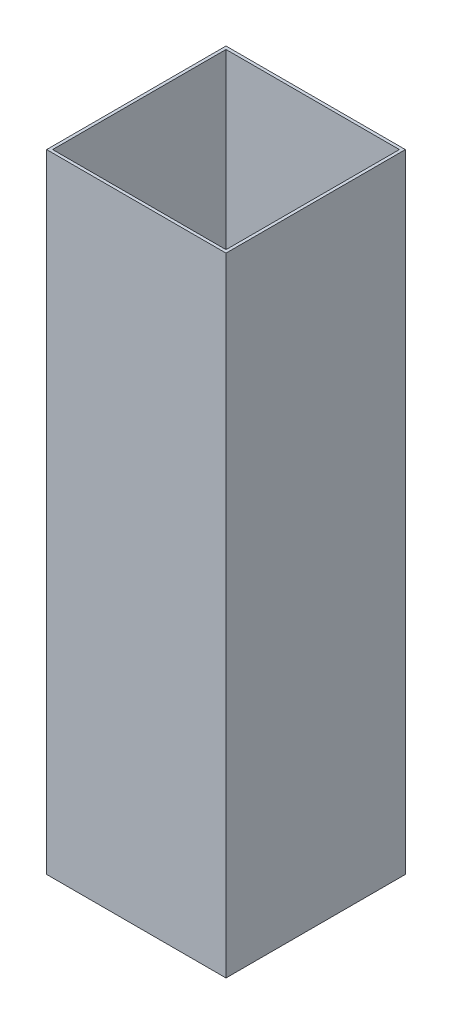
SolidWorks part; units mm, degrees
ref_plane "Front Plane" through (0, 0, 0) normal (0, 0, 1) x (1, 0, 0)
ref_plane "Top Plane" through (0, 0, 0) normal (0, 1, 0) x (1, 0, 0)
ref_plane "Right Plane" through (0, 0, 0) normal (1, 0, 0) x (0, 0, -1)
sketch "Sketch1" plane through (0, 0, 0) normal (0, 1, 0) x (1, 0, 0)
  line L0 (10, 10) -> (590, 10)
  line L1 (0, 0) -> (600, 0)
  line L2 (0, 0) -> (0, 600)
  line L3 (0, 600) -> (600, 600)
  line L4 (600, 0) -> (600, 600)
  line L5 (590, 10) -> (590, 590)
  line L6 (10, 590) -> (590, 590)
  line L7 (10, 10) -> (10, 590)
  dimension "D1" = 600
  dimension "D2" = 600
  dimension "D3" = 10
extrude "Extrude1" add sketch "Sketch1" along normal blind 2100
